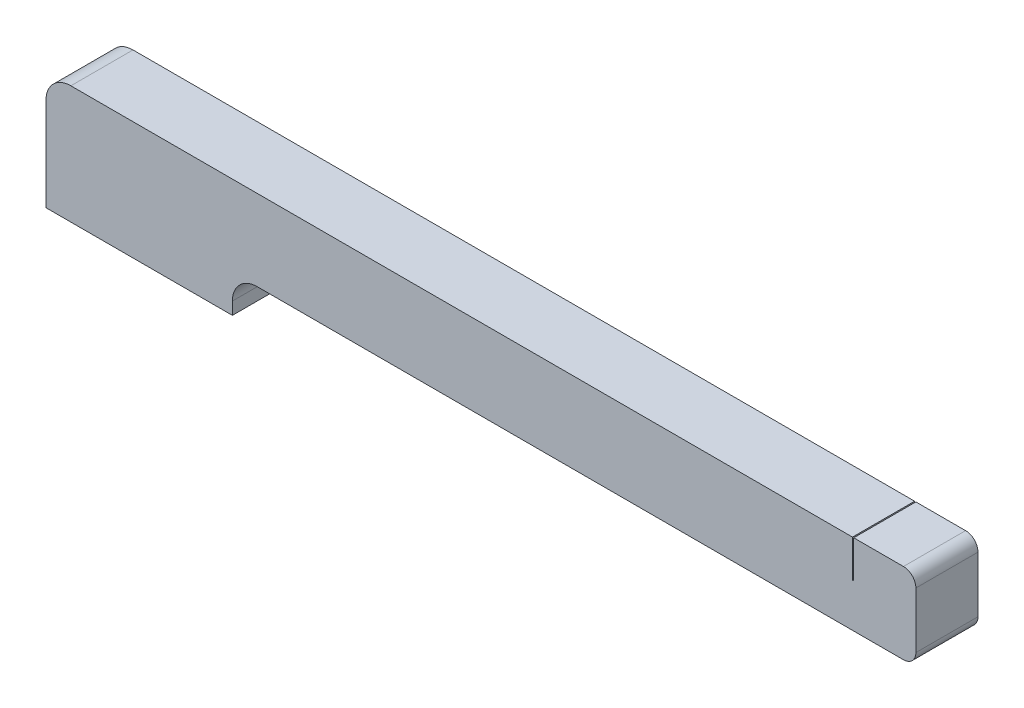
SolidWorks part; units mm, degrees
ref_plane "Front Plane" through (0, 0, 0) normal (0, 0, 1) x (1, 0, 0)
ref_plane "Top Plane" through (0, 0, 0) normal (0, 1, 0) x (1, 0, 0)
ref_plane "Right Plane" through (0, 0, 0) normal (1, 0, 0) x (0, 0, -1)
sketch "Sketch1" plane through (0, 0, 0) normal (0, 0, 1) x (1, 0, 0)
  line L0 (0, 0) -> (0, 7.5)
  line L1 (2, 9.5) -> (69, 9.5)
  line L2 (70, 8.5) -> (70, 4)
  line L3 (69, 3) -> (17, 3)
  line L4 (15, 1) -> (15, 0)
  line L5 (15, 0) -> (11, 0)
  line L9 (4, 0) -> (0, 0)
  line L10 (4, 0) -> (11, 0)
  arc A0 (17, 3) -> (15, 1) centre (17, 1) ccw
  arc A1 (2, 9.5) -> (0, 7.5) centre (2, 7.5) ccw
  arc A2 (70, 8.5) -> (69, 9.5) centre (69, 8.5) ccw
  arc A3 (69, 3) -> (70, 4) centre (69, 4) ccw
  point P11 (0, 9.5)
  point P14 (70, 9.5)
  point P17 (70, 3)
  dimension "D5" = 2
  dimension "D6" = 2
  dimension "D7" = 1
  dimension "D2" = 15
  dimension "D3" = 6.5
  dimension "D4" = 70
extrude "Boss-Extrude1" add sketch "Sketch1" along normal blind 5
sketch "Sketch3" plane through (0, 9.5, 0) normal (0, 1, 0) x (1, 0, 0)
  line L0 (0, -2.5) -> (64.95, -2.5) construction
  line L1 (0, -5) -> (0, 0) construction
  line L2 (69, 0) -> (2, 0) construction
  line L3 (64.9, -5) -> (65, -5)
  line L4 (64.9, -5) -> (64.9, 0)
  line L5 (64.9, 0) -> (65, 0)
  line L6 (65, -5) -> (65, 0)
  line L7 (64.9, -5) -> (65, 0) construction
  line L8 (64.9, 0) -> (65, -5) construction
  dimension "D1" = 64.95
  dimension "D2" = 0.1
extrude "Cut-Extrude1" cut sketch "Sketch3" against normal blind 3
equation "\"A.L\"= 0.07m"
equation "\"A.h\"= 0.007m"
equation "\"A.d\"= 0.005m"
equation "\"A.delta\"= 45.0001"
equation "\"A.w\"= 0m"
equation "\"A.v\"= 0.013m"
equation "\"A.s\"= 0.014m"
equation "\"A.t\"= 0.007m"
equation "\"B.L\"= 0.065m"
equation "\"B.h\"= 0.008m"
equation "\"B.s\"= 0.016m"
equation "\"B.t\"= 0.008m"
equation "\"C.h\"= 0.0065m"
equation "\"C.d\"= 0.005m"
equation "\"C.L\"= 0.05m"
equation "\"C.wmax\"= 0.003m"
equation "\"D.L\"= 0.06m"
equation "\"D.h\"= 0.008m"
equation "\"D.s\"= 0.012m"
equation "\"D.t\"= 0.008m"
equation "\"a_h\"= 0.0001m"
equation "\"a_d\"= 0.005m"
equation "\"a_L\"= 0.008m"
equation "\"b_h\"= 0.0004m"
equation "\"b_d\"= 0.005m"
equation "\"b_L\"= 0.007m"
equation "\"c_h\"= 0.0001m"
equation "\"c_d\"= 0.005m"
equation "\"c_L\"= 0.01m"
equation "\"d_h\"= 0.0001m"
equation "\"d_d\"= 0.005m"
equation "\"d_L\"= 0.01m"
equation "\"S.h\"= 0.015m"
equation "\"S.L\"= 0.09275m"
equation "\"D1@Sketch1\"=\"C.h\"+\"C.wmax\""
equation "\"D2@Sketch1\"=\"S.h\""
equation "\"D3@Sketch1\"=\"C.h\""
equation "\"D4@Sketch1\"=\"C.L\"+\"S.h\"+0.005"
equation "\"D1@Boss-Extrude1\"=0.005m"
equation "\"D1@Sketch3\"=\"C.L\"+\"S.h\"-\"c_h\"/2"
equation "\"D2@Sketch3\"=\"c_h\""
